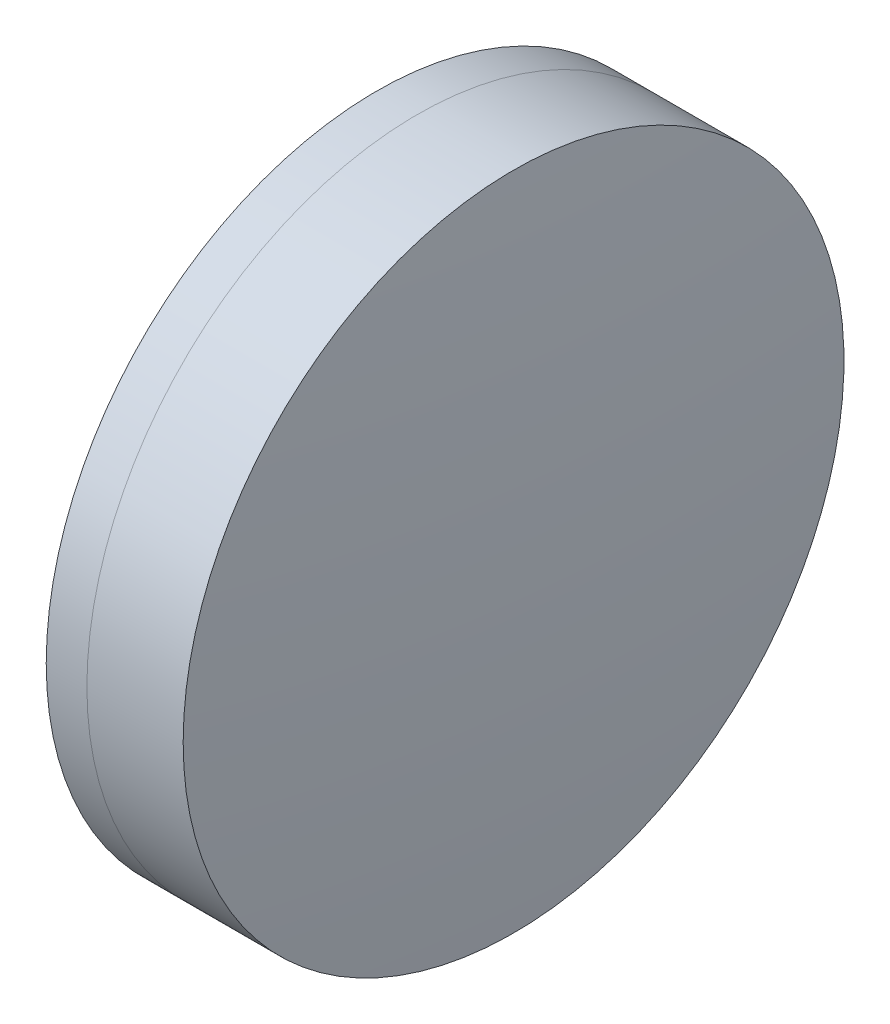
SolidWorks part; units mm, degrees
ref_plane "前视基准面" through (0, 0, 0) normal (0, 0, 1) x (1, 0, 0)
ref_plane "上视基准面" through (0, 0, 0) normal (0, 1, 0) x (1, 0, 0)
ref_plane "右视基准面" through (0, 0, 0) normal (1, 0, 0) x (0, 0, -1)
sketch "草图1" plane through (0, 0, 0) normal (0, 1, 0) x (1, 0, 0)
  line L0 (-9.7026, 0) -> (69.6628, 0) construction
  line L1 (58.6712, -12.5) -> (60.2098, -12.5)
  line L2 (58.6712, 12.5) -> (60.2098, 12.5)
  arc A0 (60.2098, -12.5) -> (60.2098, 12.5) centre (14.8797, 0) ccw
  arc A1 (58.6712, 12.5) -> (58.6712, -12.5) centre (120.5677, 0) ccw
  point P4 (69.6628, 0)
  point P10 (57.4217, 0)
  point P11 (61.9017, 0)
  dimension "D3" = 63.146
  dimension "D4" = 47.022
  dimension "D1" = 12.5
  dimension "D2" = 12.5
  dimension "D5" = 4.48
revolve "旋转1" add sketch "草图1" angle 360 about L0
sketch "草图2" plane through (0, 0, 0) normal (0, 1, 0) x (1, 0, 0)
  line L0 (-0.5519, 0) -> (70.9822, 0) construction
  line L2 (60.2098, 12.5) -> (63.8524, 12.5)
  line L3 (60.2098, -12.5) -> (63.8524, -12.5)
  arc A0 (63.8524, -12.5) -> (63.8524, 12.5) centre (-78.1033, 0) ccw
  arc A1 (60.2098, -12.5) -> (60.2098, 12.5) centre (14.8797, 0) ccw construction
  arc A2 (60.2098, -12.5) -> (60.2098, 12.5) centre (14.8797, 0) ccw
  point P4 (61.9017, 0)
  point P8 (64.4017, 0)
  point P9 (70.9822, 0)
  dimension "D1" = 142.505
  dimension "D2" = 2.5
revolve "旋转3" add sketch "草图2" angle 360 about L0
